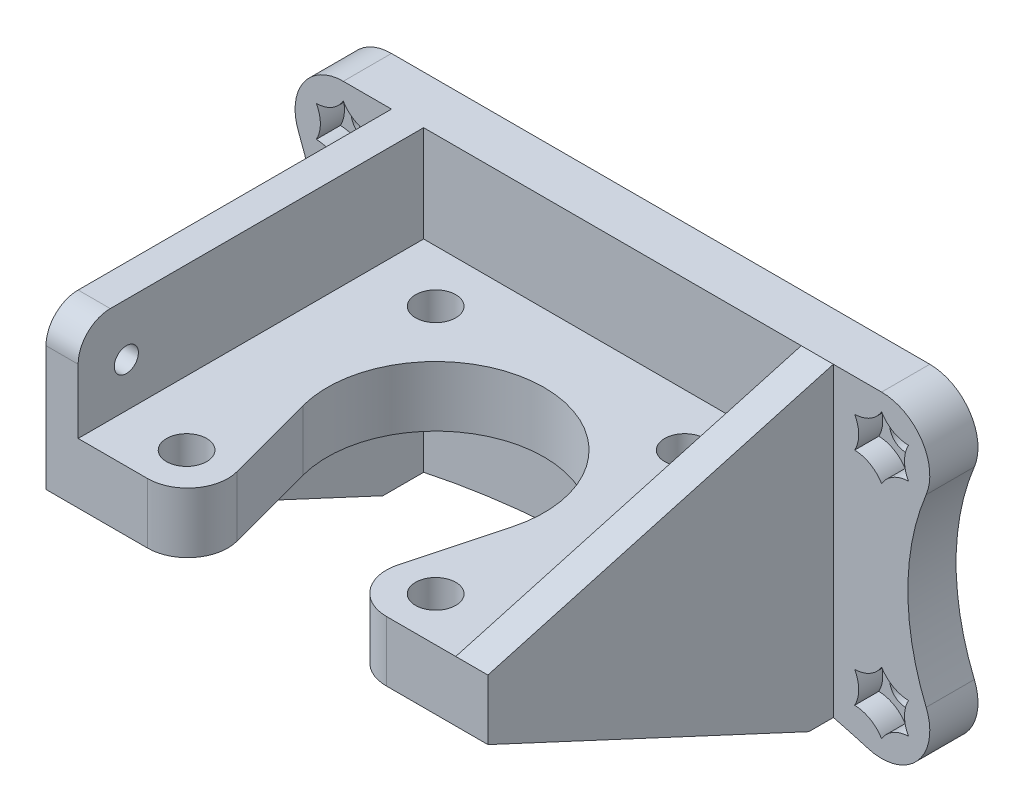
SolidWorks part; units mm, degrees
ref_plane "Front Plane" through (0, 0, 0) normal (0, 0, 1) x (1, 0, 0)
ref_plane "Top Plane" through (0, 0, 0) normal (0, 1, 0) x (1, 0, 0)
ref_plane "Right Plane" through (0, 0, 0) normal (1, 0, 0) x (0, 0, -1)
sketch "Sketch1" plane through (0, 0, 0) normal (0, 0, 1) x (1, 0, 0)
  line L0 (4, 7.5) -> (4, 19.5)
  line L5 (0, 0) -> (55, 0)
  line L7 (4, 7.5) -> (55, 7.5)
  line L8 (55, 0) -> (55, 7.5)
  line L9 (0, 19.5) -> (4, 19.5)
  line L12 (0, 19.5) -> (0, 0)
  dimension "D1" = 51
  dimension "D2" = 12
  dimension "D3" = 4
  dimension "D6" = 7.5
extrude "Boss-Extrude1" add sketch "Sketch1" along normal blind 49
sketch "Sketch2" plane through (0, 7.5, 0) normal (0, 1, 0) x (1, 0, 0)
  line L0 (55, -49) -> (4, -49) construction
  line L1 (55, -49) -> (55, 0) construction
  line L2 (43, -12.5) -> (12, -43.5) construction
  line L3 (14.46, -31.4941) -> (19.1507, -49)
  line L4 (19.1507, -49) -> (35.8493, -49)
  line L5 (35.8493, -49) -> (40.54, -31.4941)
  line L6 (27.5, -28) -> (27.5, -40.6945) construction
  arc A0 (40.54, -31.4941) -> (14.46, -31.4941) centre (27.5, -28) ccw
  circle A1 centre (12, -12.5) radius 2.5
  circle A2 centre (43, -12.5) radius 2.5
  circle A3 centre (12, -43.5) radius 2.5
  circle A4 centre (43, -43.5) radius 2.5
  dimension "D3" = 27
  dimension "D6" = 5
  dimension "D1" = 21
  dimension "D2" = 27.5
  dimension "D4" = 31
  dimension "D5" = 31
  dimension "D7" = 15
  dimension "D8" = 15
extrude "Cut-Extrude1" cut sketch "Sketch2" against normal through all
sketch "Sketch4" plane through (0, 0, 0) normal (0, 0, -1) x (-1, 0, 0)
  line L1 (12, -20) -> (-67, -20)
  line L2 (12, -20) -> (12, 19.5)
  line L3 (12, 19.5) -> (-67, 19.5)
  line L4 (-67, -20) -> (-67, 19.5)
  line L5 (-4, 19.5) -> (0, 19.5) construction
  line L6 (0, 19.5) -> (0, 0) construction
  line L8 (-55, 0) -> (-55, 7.5) construction
  line L9 (0, 0) -> (-55, 0) construction
  dimension "D1" = 12
  dimension "D2" = 20
  dimension "D3" = 12
extrude "Boss-Extrude2" add sketch "Sketch4" against normal blind 6
sketch "Sketch6" plane through (0, 0, 0) normal (-1, 0, 0) x (0, 0, 1)
  line L0 (6, -20) -> (49, 0)
  line L1 (49, 0) -> (6, 0)
  line L2 (6, 0) -> (6, -20)
  line L4 (49, 19.5) -> (49, 0) construction
extrude "Boss-Extrude3" add sketch "Sketch6" against normal up to surface (4 mm away) up to face at (4, 13.5, 27.5)
sketch "Sketch5" plane through (0, 0, 0) normal (0, 0, -1) x (-1, 0, 0)
  line L1 (12, -20) -> (12, 19.5) construction
  line L4 (-67, -20) -> (12, -20) construction
  line L5 (-67, 19.5) -> (12, 19.5) construction
  line L6 (-67, 19.5) -> (-67, -20) construction
  circle A0 centre (-61, 13.5) radius 2
  circle A1 centre (-61, -14) radius 2
  circle A2 centre (6, 13.5) radius 2
  circle A3 centre (6, -14) radius 2
  dimension "D5" = 4
  dimension "D1" = 6
  dimension "D2" = 6
  dimension "D3" = 6
  dimension "D4" = 6
extrude "Cut-Extrude3" cut sketch "Sketch5" against normal blind 10
sketch "Sketch7" plane through (55, 0, 0) normal (1, 0, 0) x (0, 0, -1)
  line L0 (-49, 7.5) -> (-6, 19.5)
  line L1 (-6, 19.5) -> (0, 19.5)
  line L2 (0, 19.5) -> (0, -20)
  line L3 (0, -20) -> (-6, -20)
  line L4 (-6, -20) -> (-49, 0)
  line L5 (-49, 0) -> (-49, 7.5)
  line L6 (-6, 19.5) -> (-6, -20) construction
  line L7 (-6, 19.5) -> (0, 19.5) construction
  line L8 (-6, -20) -> (0, -20) construction
  line L9 (0, 19.5) -> (0, -20) construction
extrude "Boss-Extrude4" add sketch "Sketch7" against normal blind 4
sketch "Sketch8" plane through (0, 0, 0) normal (-1, 0, 0) x (0, 0, 1)
  line L0 (49, 19.5) -> (49, 0) construction
  line L2 (49, 19.5) -> (6, 19.5) construction
  circle A0 centre (43, 13) radius 1.5
  circle A1 centre (43, 3.5) radius 1.5
  dimension "D4" = 3
  dimension "D1" = 9.5
  dimension "D2" = 6
  dimension "D3" = 16
extrude "Cut-Extrude4" cut sketch "Sketch8" against normal blind 8
fillet "Fillet1" radius 6 4 edges at (67, 19.5, 3) (67, -20, 3) (-12, -20, 3) (-12, 19.5, 3)
fillet "Fillet2" radius 5 2 edges at (35.8493, 3.75, 49) (19.1507, 3.75, 49)
sketch "Sketch9" plane through (0, 0, 6) normal (0, 0, 1) x (1, 0, 0)
  line L1 (-6, 16.7909) -> (-8.85, 15.1454)
  line L2 (-8.85, 15.1454) -> (-8.85, 11.8546)
  line L3 (-8.85, 11.8546) -> (-6, 10.2091)
  line L4 (-6, 10.2091) -> (-3.15, 11.8546)
  line L5 (-3.15, 11.8546) -> (-3.15, 15.1454)
  line L6 (-3.15, 15.1454) -> (-6, 16.7909)
  line L7 (-6, -10.7091) -> (-8.85, -12.3546)
  line L8 (-8.85, -12.3546) -> (-8.85, -15.6454)
  line L9 (-8.85, -15.6454) -> (-6, -17.2909)
  line L10 (-6, -17.2909) -> (-3.15, -15.6454)
  line L11 (-3.15, -15.6454) -> (-3.15, -12.3546)
  line L12 (-3.15, -12.3546) -> (-6, -10.7091)
  line L13 (61, -10.7091) -> (58.15, -12.3546)
  line L14 (58.15, -12.3546) -> (58.15, -15.6454)
  line L15 (58.15, -15.6454) -> (61, -17.2909)
  line L16 (61, -17.2909) -> (63.85, -15.6454)
  line L17 (63.85, -15.6454) -> (63.85, -12.3546)
  line L18 (63.85, -12.3546) -> (61, -10.7091)
  line L19 (61, 10.2091) -> (63.85, 11.8546)
  line L20 (63.85, 11.8546) -> (63.85, 15.1454)
  line L21 (63.85, 15.1454) -> (61, 16.7909)
  line L22 (61, 16.7909) -> (58.15, 15.1454)
  line L23 (58.15, 15.1454) -> (58.15, 11.8546)
  line L24 (58.15, 11.8546) -> (61, 10.2091)
  circle A0 centre (-6, 13.5) radius 2.85 construction
  circle A1 centre (-6, -14) radius 2.85 construction
  circle A2 centre (61, -14) radius 2.85 construction
  circle A3 centre (61, 13.5) radius 2.85 construction
  dimension "D1" = 5.7
extrude "Cut-Extrude5" cut sketch "Sketch9" against normal blind 3
sketch "Sketch10" plane through (0, 0, 0) normal (0, 0, -1) x (-1, 0, 0)
  line L0 (-61, 19.5) -> (-61, 26.1947)
  line L1 (-61, 26.1947) -> (-93.2137, 26.1947)
  line L2 (-93.2137, 26.1947) -> (-93.2137, -32.4835)
  line L3 (-93.2137, -32.4835) -> (20.6568, -32.4835)
  line L4 (20.6568, -32.4835) -> (20.6568, 27.2405)
  line L5 (20.6568, 27.2405) -> (6, 27.2405)
  line L6 (6, 27.2405) -> (6, 19.5)
  arc A0 (-61, 19.5) -> (-67, 13.5) centre (-61, 13.5) ccw construction
  arc A1 (-67, -14) -> (-61, -20) centre (-61, -14) ccw construction
  arc A2 (6, -20) -> (12, -14) centre (6, -14) ccw construction
  arc A3 (12, 13.5) -> (6, 19.5) centre (6, 13.5) ccw construction
  arc A4 (-61, 19.5) -> (-66.5451, 11.2083) centre (-61, 13.5) ccw
  arc A5 (-66.5451, -11.7083) -> (-59.3038, -19.7552) centre (-61, -14) ccw
  arc A6 (4.3038, -19.7552) -> (11.5451, -11.7083) centre (6, -14) ccw
  arc A7 (11.5451, 11.2083) -> (6, 19.5) centre (6, 13.5) ccw
  arc A8 (-66.5451, -11.7083) -> (-66.5451, 11.2083) centre (-94.2707, -0.25) ccw
  arc A9 (11.5451, 11.2083) -> (11.5451, -11.7083) centre (39.2707, -0.25) ccw
  arc A10 (4.3038, -19.7552) -> (-59.3038, -19.7552) centre (-27.5, -127.6662) ccw
  dimension "D1" = 30
  dimension "D2" = 112.5
extrude "Cut-Extrude6" cut sketch "Sketch10" against normal through all
fillet "Fillet3" radius 4 1 edges at (2, 19.5, 49)
sketch "Sketch11" plane through (0, 0, 6) normal (0, 0, 1) x (1, 0, 0)
  line L0 (-6, 16.7909) -> (-8.85, 15.1454) construction
  line L1 (-6, 17.3682) -> (-9.35, 15.4341) construction
  line L2 (-9.35, 15.4341) -> (-9.35, 11.5659) construction
  line L3 (-9.35, 11.5659) -> (-6, 9.6318) construction
  line L4 (-6, 9.6318) -> (-2.65, 11.5659) construction
  line L5 (-2.65, 11.5659) -> (-2.65, 15.4341) construction
  line L6 (-2.65, 15.4341) -> (-6, 17.3682) construction
  line L7 (-8.85, 15.1454) -> (-8.85, 11.8546) construction
  line L8 (-8.85, 11.8546) -> (-6, 10.2091) construction
  line L9 (-6, 10.2091) -> (-3.15, 11.8546) construction
  line L10 (-3.15, 11.8546) -> (-3.15, 15.1454) construction
  line L11 (-3.15, 15.1454) -> (-6, 16.7909) construction
  circle A0 centre (-6, 13.5) radius 3.35 construction
  arc A1 (-9.35, 15.4341) -> (-9.35, 11.5659) centre (-12.8408, 13.5) cw
  arc A2 (-9.35, 11.5659) -> (-6, 9.6318) centre (-9.4204, 7.5757) cw
  arc A3 (-6, 9.6318) -> (-2.65, 11.5659) centre (-2.5796, 7.5757) cw
  arc A4 (-2.65, 11.5659) -> (-2.65, 15.4341) centre (0.8408, 13.5) cw
  arc A5 (-6, 17.3682) -> (-2.65, 15.4341) centre (-2.5796, 19.4243) ccw
  arc A6 (-6, 17.3682) -> (-9.35, 15.4341) centre (-9.4204, 19.4243) cw
  dimension "D1" = 6.7
extrude "Cut-Extrude7" cut sketch "Sketch11" against normal up to surface (3 mm away) up to face at (-6, 13.5, 3)
pattern_linear "LPattern1" count 2 spacing 67 along (1, 0, 0) count 2 spacing 27.5 along (0, -1, 0) of "Cut-Extrude7"
